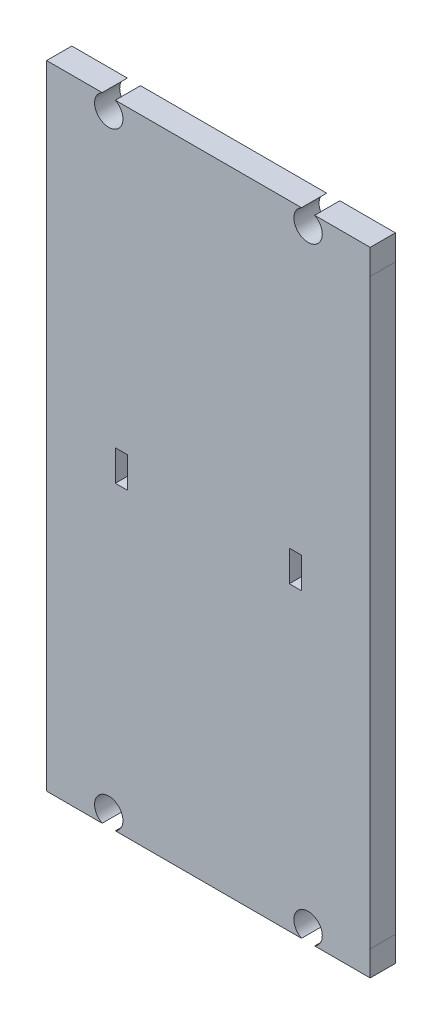
SolidWorks part; units mm, degrees
ref_plane "정면" through (0, 0, 0) normal (0, 0, 1) x (1, 0, 0)
ref_plane "윗면" through (0, 0, 0) normal (0, 1, 0) x (1, 0, 0)
ref_plane "우측면" through (0, 0, 0) normal (1, 0, 0) x (0, 0, -1)
sketch "Sketch1" plane through (0, 0, 0) normal (0, 0, 1) x (1, 0, 0)
  line L0 (-11.3467, -39.1193) -> (11.6694, -39.1197)
  line L1 (20.1622, 35.9901) -> (20.1622, 39.1001)
  line L2 (-19.8379, -36.0091) -> (-19.838, -39.1191)
  line L3 (20.1622, 35.9901) -> (20.1619, -36.0099)
  line L4 (20.1622, 39.1001) -> (13.3522, 39.1001)
  line L5 (-19.8378, 39.1001) -> (-19.8379, -36.0091)
  line L6 (0.162, 39.2936) -> (0.162, -36.0084) construction
  line L7 (-19.838, -39.1191) -> (-12.9711, -39.1193)
  line L8 (10.162, -0.0084) -> (10.162, -1.9134)
  line L9 (10.162, -1.9134) -> (11.672, -1.9134)
  line L10 (11.672, -1.9134) -> (11.672, 1.8966)
  line L11 (11.672, 1.8966) -> (10.162, 1.8966)
  line L12 (10.162, 1.8966) -> (10.162, -0.0084)
  line L13 (-9.838, 1.8966) -> (-9.838, -0.0084)
  line L14 (-11.348, 1.8966) -> (-9.838, 1.8966)
  line L15 (-11.348, -1.9134) -> (-11.348, 1.8966)
  line L16 (-9.838, -1.9134) -> (-11.348, -1.9134)
  line L17 (-9.838, -0.0084) -> (-9.838, -1.9134)
  line L18 (20.1618, -39.1199) -> (20.1619, -36.0099)
  line L19 (20.162, -0.0099) -> (-19.838, -0.0095) construction
  line L20 (11.6701, 39.1001) -> (-11.346, 39.1001)
  line L21 (-12.9704, 39.1001) -> (-19.8378, 39.1001)
  line L22 (13.2938, -39.1198) -> (20.1618, -39.1199)
  line L23 (13.3522, 39.1001) -> (13.2945, 39.1001)
  arc A0 (-12.9704, 39.1001) -> (-11.346, 39.1001) centre (-12.1582, 37.5444) ccw
  arc A1 (13.2945, 39.1001) -> (11.6701, 39.1001) centre (12.4823, 37.5444) cw
  arc A2 (13.2938, -39.1198) -> (11.6694, -39.1197) centre (12.4816, -37.564) ccw
  arc A3 (-12.9711, -39.1193) -> (-11.3467, -39.1193) centre (-12.1589, -37.5635) cw
  dimension "D1" = 3.11
extrude "Boss-Extrude1" add sketch "Sketch1" along normal blind 3.1115
